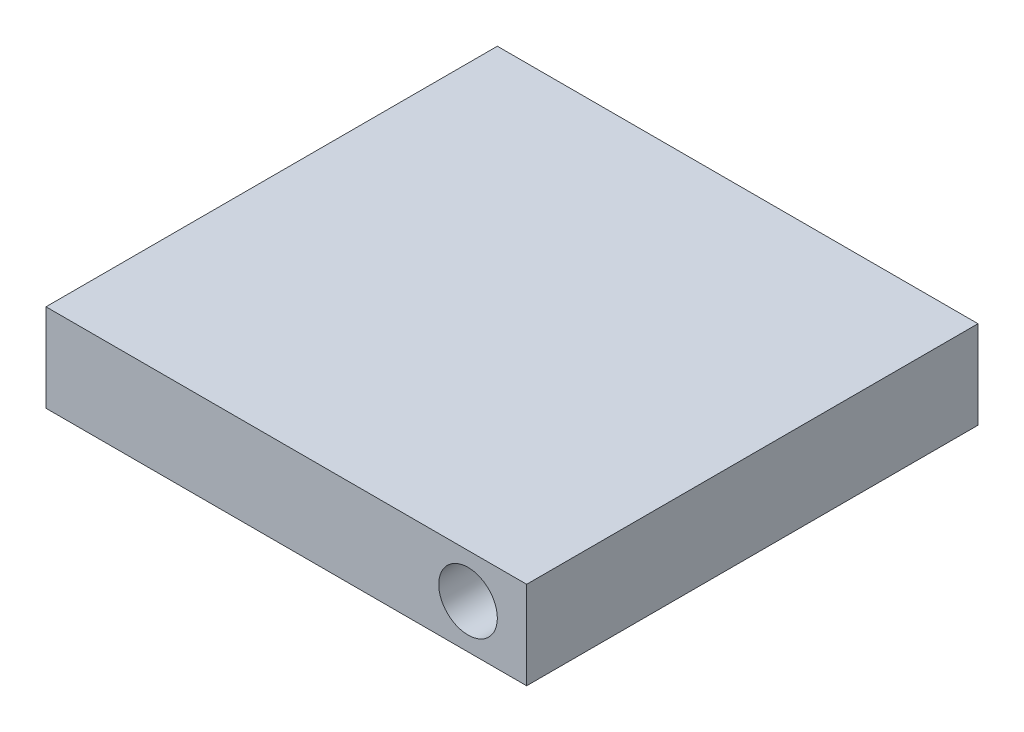
SolidWorks part; units mm, degrees
ref_plane "Alzado" through (0, 0, 0) normal (0, 0, 1) x (1, 0, 0)
ref_plane "Planta" through (0, 0, 0) normal (0, 1, 0) x (1, 0, 0)
ref_plane "Vista lateral" through (0, 0, 0) normal (1, 0, 0) x (0, 0, -1)
sketch "Croquis1" plane through (0, 0, 0) normal (0, 1, 0) x (1, 0, 0)
  line L1 (0, 0) -> (2, 0)
  line L2 (0, 0) -> (0, -2)
  line L3 (0, -2) -> (2, -2)
  line L4 (2, 0) -> (2, -2)
  dimension "D1" = 2
  dimension "D2" = 2
extrude "Saliente-Extruir1" add sketch "Croquis1" along normal blind 0.2
sketch "Croquis2" plane through (0, 0.2, 0) normal (0, 1, 0) x (1, 0, 0)
  line L0 (2, 0) -> (0, 0) construction
  line L1 (-0.3, 0.3) -> (2.3, 0.3)
  line L2 (-0.3, 0.3) -> (-0.3, -2.3)
  line L3 (-0.3, -2.3) -> (2.3, -2.3)
  line L4 (2.3, 0.3) -> (2.3, -2.3)
  line L6 (0, 0) -> (0, -2) construction
  line L7 (2, -2) -> (2, 0) construction
  line L8 (0, -2) -> (2, -2) construction
  dimension "D1" = 0.3
  dimension "D2" = 0.3
  dimension "D3" = 0.3
  dimension "D4" = 0.3
extrude "Saliente-Extruir2" add sketch "Croquis2" along normal blind 0.2
sketch "Croquis3" plane through (0, 0.4, 0) normal (0, 1, 0) x (1, 0, 0)
  line L0 (-0.3, 0.3) -> (-0.3, -2.3) construction
  line L1 (-0.6, 0.6) -> (2.6, 0.6)
  line L2 (-0.6, 0.6) -> (-0.6, -2.6)
  line L3 (-0.6, -2.6) -> (2.6, -2.6)
  line L4 (2.6, 0.6) -> (2.6, -2.6)
  line L5 (2.3, 0.3) -> (-0.3, 0.3) construction
  line L6 (2.3, -2.3) -> (2.3, 0.3) construction
  line L7 (-0.3, -2.3) -> (2.3, -2.3) construction
  dimension "D1" = 0.3
  dimension "D2" = 0.3
  dimension "D3" = 0.3
  dimension "D4" = 0.3
extrude "Saliente-Extruir3" add sketch "Croquis3" along normal blind 0.2
sketch "Croquis4" plane through (0, 0.6, 0) normal (0, 1, 0) x (1, 0, 0)
  line L0 (2.6, 0.6) -> (-0.6, 0.6) construction
  line L1 (-0.9, 0.9) -> (2.9, 0.9)
  line L2 (-0.9, 0.9) -> (-0.9, -2.9)
  line L3 (-0.9, -2.9) -> (2.9, -2.9)
  line L4 (2.9, 0.9) -> (2.9, -2.9)
  line L5 (-0.6, 0.6) -> (-0.6, -2.6) construction
  line L6 (2.6, -2.6) -> (2.6, 0.6) construction
  line L7 (-0.6, -2.6) -> (2.6, -2.6) construction
  dimension "D1" = 0.3
  dimension "D2" = 0.3
  dimension "D3" = 0.3
  dimension "D4" = 0.3
extrude "Saliente-Extruir4" add sketch "Croquis4" along normal blind 0.2
sketch "Croquis5" plane through (0, 0.8, 0) normal (0, 1, 0) x (1, 0, 0)
  line L0 (2.9, 0.9) -> (-0.9, 0.9) construction
  line L1 (-1.2, 1.2) -> (3.2, 1.2)
  line L2 (-1.2, 1.2) -> (-1.2, -3.2)
  line L3 (-1.2, -3.2) -> (3.2, -3.2)
  line L4 (3.2, 1.2) -> (3.2, -3.2)
  line L5 (-0.9, 0.9) -> (-0.9, -2.9) construction
  line L6 (-0.9, -2.9) -> (2.9, -2.9) construction
  line L7 (2.9, -2.9) -> (2.9, 0.9) construction
  dimension "D1" = 0.3
  dimension "D2" = 0.3
  dimension "D3" = 0.3
  dimension "D4" = 0.3
extrude "Saliente-Extruir5" add sketch "Croquis5" along normal blind 0.2
sketch "Croquis6" plane through (0, 1, 0) normal (0, 1, 0) x (1, 0, 0)
  line L0 (3.2, 1.2) -> (-1.2, 1.2) construction
  line L1 (-1.5, 1.5) -> (3.5, 1.5)
  line L2 (-1.5, 1.5) -> (-1.5, -3.5)
  line L3 (-1.5, -3.5) -> (3.5, -3.5)
  line L4 (3.5, 1.5) -> (3.5, -3.5)
  line L5 (-1.2, 1.2) -> (-1.2, -3.2) construction
  line L6 (3.2, -3.2) -> (3.2, 1.2) construction
  line L7 (-1.2, -3.2) -> (3.2, -3.2) construction
  dimension "D1" = 0.3
  dimension "D2" = 0.3
  dimension "D3" = 0.3
  dimension "D4" = 0.3
extrude "Saliente-Extruir6" add sketch "Croquis6" along normal blind 0.2
sketch "Croquis7" plane through (0, 1.2, 0) normal (0, 1, 0) x (1, 0, 0)
  line L0 (3.5, 1.5) -> (-1.5, 1.5) construction
  line L1 (-1.8, 1.8) -> (3.8, 1.8)
  line L2 (-1.8, 1.8) -> (-1.8, -3.8)
  line L3 (-1.8, -3.8) -> (3.8, -3.8)
  line L4 (3.8, 1.8) -> (3.8, -3.8)
  line L5 (-1.5, 1.5) -> (-1.5, -3.5) construction
  line L6 (-1.5, -3.5) -> (3.5, -3.5) construction
  line L7 (3.5, -3.5) -> (3.5, 1.5) construction
  dimension "D1" = 0.3
  dimension "D2" = 0.3
  dimension "D3" = 0.3
  dimension "D4" = 0.3
extrude "Saliente-Extruir7" add sketch "Croquis7" along normal blind 0.2
sketch "Croquis8" plane through (0, 1.4, 0) normal (0, 1, 0) x (1, 0, 0)
  line L0 (3.8, 1.8) -> (-1.8, 1.8) construction
  line L1 (-2.1, 2.1) -> (4.1, 2.1)
  line L2 (-2.1, 2.1) -> (-2.1, -4.1)
  line L3 (-2.1, -4.1) -> (4.1, -4.1)
  line L4 (4.1, 2.1) -> (4.1, -4.1)
  line L5 (-1.8, 1.8) -> (-1.8, -3.8) construction
  line L6 (-1.8, -3.8) -> (3.8, -3.8) construction
  line L7 (3.8, -3.8) -> (3.8, 1.8) construction
  dimension "D1" = 0.3
  dimension "D2" = 0.3
  dimension "D3" = 0.3
  dimension "D4" = 0.3
extrude "Saliente-Extruir8" add sketch "Croquis8" along normal blind 0.2
sketch "Croquis9" plane through (0, 1.6, 0) normal (0, 1, 0) x (1, 0, 0)
  line L0 (4.1, 2.1) -> (-2.1, 2.1) construction
  line L1 (-2.4, 2.4) -> (4.4, 2.4)
  line L2 (-2.4, 2.4) -> (-2.4, -4.4)
  line L3 (-2.4, -4.4) -> (4.4, -4.4)
  line L4 (4.4, 2.4) -> (4.4, -4.4)
  line L5 (-2.1, 2.1) -> (-2.1, -4.1) construction
  line L6 (-2.1, -4.1) -> (4.1, -4.1) construction
  line L7 (4.1, -4.1) -> (4.1, 2.1) construction
  dimension "D1" = 0.3
  dimension "D2" = 0.3
  dimension "D3" = 0.3
  dimension "D4" = 0.3
extrude "Saliente-Extruir9" add sketch "Croquis9" along normal blind 0.2
sketch "Croquis10" plane through (0, 1.8, 0) normal (0, 1, 0) x (1, 0, 0)
  line L0 (4.4, 2.4) -> (-2.4, 2.4) construction
  line L1 (-2.7, 2.7) -> (4.7, 2.7)
  line L2 (-2.7, 2.7) -> (-2.7, -4.7)
  line L3 (-2.7, -4.7) -> (4.7, -4.7)
  line L4 (4.7, 2.7) -> (4.7, -4.7)
  line L5 (4.4, -4.4) -> (4.4, 2.4) construction
  line L6 (-2.4, -4.4) -> (4.4, -4.4) construction
  line L7 (-2.4, 2.4) -> (-2.4, -4.4) construction
  dimension "D1" = 0.3
  dimension "D2" = 0.3
  dimension "D3" = 0.3
  dimension "D4" = 0.3
extrude "Saliente-Extruir10" add sketch "Croquis10" along normal blind 0.2
sketch "Croquis11" plane through (0, 2, 0) normal (0, 1, 0) x (1, 0, 0)
  line L0 (4.7, 2.7) -> (-2.7, 2.7) construction
  line L1 (-6.7, 6.7) -> (9.7, 6.7)
  line L2 (-6.7, 6.7) -> (-6.7, -8.7)
  line L3 (-6.7, -8.7) -> (9.7, -8.7)
  line L4 (9.7, 6.7) -> (9.7, -8.7)
  line L5 (-2.7, 2.7) -> (-2.7, -4.7) construction
  line L6 (-2.7, -4.7) -> (4.7, -4.7) construction
  line L7 (4.7, -4.7) -> (4.7, 2.7) construction
  dimension "D1" = 4
  dimension "D2" = 4
  dimension "D3" = 4
  dimension "D4" = 5
extrude "Saliente-Extruir11" add sketch "Croquis11" along normal blind 3
sketch "Croquis12" plane through (0, 0, 8.7) normal (0, 0, 1) x (1, 0, 0)
  line L0 (-6.7, 5) -> (9.7, 5) construction
  line L1 (9.7, 5) -> (9.7, 2) construction
  circle A0 centre (7.7, 3.5) radius 1
  dimension "D1" = 1.5
  dimension "D2" = 2
extrude "Cortar-Extruir1" cut sketch "Croquis12" against normal through all
equation "\"h\" = 0.2"
equation "\"D1@Saliente-Extruir1\" = \"nlayer\" * \"h\""
equation "\"D1@Saliente-Extruir2\"= \"nlayer\" * \"h\""
equation "\"D1@Saliente-Extruir3\" = \"nlayer\" * \"h\""
equation "\"D1@Saliente-Extruir4\" = \"nlayer\" * \"h\""
equation "\"D1@Saliente-Extruir5\" = \"nlayer\" * \"h\""
equation "\"D1@Saliente-Extruir6\" = \"nlayer\" * \"h\""
equation "\"D1@Saliente-Extruir7\" = \"nlayer\" * \"h\""
equation "\"D1@Saliente-Extruir8\" = \"nlayer\" * \"h\""
equation "\"D1@Saliente-Extruir9\" = \"nlayer\" * \"h\""
equation "\"D1@Saliente-Extruir10\"= \"nlayer\" * \"h\""
equation "\"y\"= 0.3"
equation "\"D1@Croquis2\"=\"y\""
equation "\"x\"= 0.3"
equation "\"D2@Croquis2\"=\"x\""
equation "\"D4@Croquis2\"=\"y\""
equation "\"D3@Croquis2\"=\"x\""
equation "\"D2@Croquis3\"=\"y\""
equation "\"D1@Croquis3\"=\"x\""
equation "\"D4@Croquis3\"=\"y\""
equation "\"D3@Croquis3\"=\"x\""
equation "\"D1@Croquis4\"=\"y\""
equation "\"D2@Croquis4\"=\"x\""
equation "\"D3@Croquis4\"=\"x\""
equation "\"D4@Croquis4\"=\"y\""
equation "\"D1@Croquis5\"=\"y\""
equation "\"D2@Croquis5\"=\"x\""
equation "\"D3@Croquis5\"=\"y\""
equation "\"D4@Croquis5\"=\"x\""
equation "\"D1@Croquis6\"=\"y\""
equation "\"D2@Croquis6\"=\"x\""
equation "\"D4@Croquis6\"=\"y\""
equation "\"D3@Croquis6\"=\"x\""
equation "\"D1@Croquis7\"=\"y\""
equation "\"D2@Croquis7\"=\"x\""
equation "\"D3@Croquis7\"=\"y\""
equation "\"D4@Croquis7\"=\"x\""
equation "\"D1@Croquis8\"=\"y\""
equation "\"D2@Croquis8\"=\"x\""
equation "\"D4@Croquis8\"=\"x\""
equation "\"D3@Croquis8\"=\"y\""
equation "\"D1@Croquis9\"=\"y\""
equation "\"D2@Croquis9\"=\"x\""
equation "\"D3@Croquis9\"=\"y\""
equation "\"D4@Croquis9\"=\"x\""
equation "\"D1@Croquis10\"=\"y\""
equation "\"D4@Croquis10\"=\"x\""
equation "\"D3@Croquis10\"=\"y\""
equation "\"D2@Croquis10\"=\"x\""
equation "\"D1@Saliente-Extruir11\"=\"h\"*10"
equation "\"w\"= 0.4"
equation "\"l2\"=2"
equation "\"D1@Croquis1\"=\"l2\""
equation "\"nlayer\"= 1"
equation "\"l\"= 2"
equation "\"D2@Croquis1\"=\"l\""
equation "\"margin\"= 4"
equation "\"D3@Croquis11\"=\"margin\""
equation "\"D1@Croquis11\"=\"margin\""
equation "\"D2@Croquis11\"=\"margin\""
